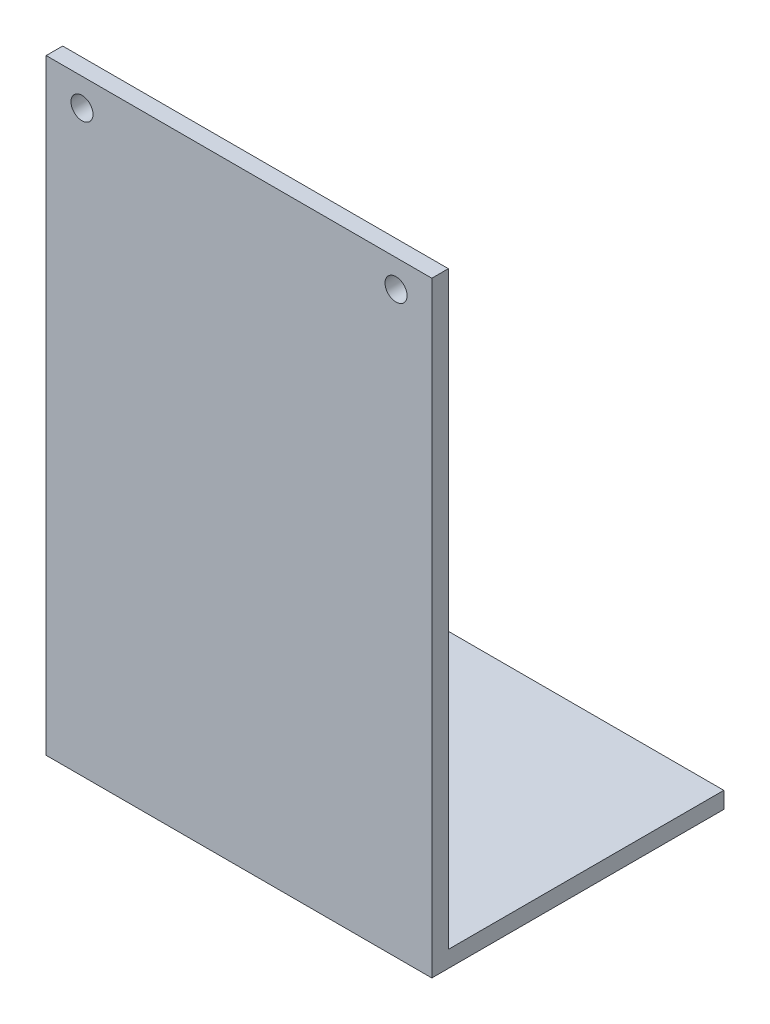
SolidWorks part; units mm, degrees
ref_plane "Front Plane" through (0, 0, 0) normal (0, 0, 1) x (1, 0, 0)
ref_plane "Top Plane" through (0, 0, 0) normal (0, 1, 0) x (1, 0, 0)
ref_plane "Right Plane" through (0, 0, 0) normal (1, 0, 0) x (0, 0, -1)
sketch "Sketch1" plane through (0, 0, 0) normal (0, 0, 1) x (1, 0, 0)
  line L1 (-35, -55) -> (35, -55)
  line L2 (-35, -55) -> (-35, 55)
  line L3 (-35, 55) -> (35, 55)
  line L4 (35, -55) -> (35, 55)
  line L5 (-35, -55) -> (35, 55) construction
  line L6 (-35, 55) -> (35, -55) construction
  point P0 (0, 0)
  dimension "D1" = 70
  dimension "D2" = 110
extrude "Boss-Extrude1" add sketch "Sketch1" along normal blind 3
sketch "Sketch2" plane through (0, 0, 0) normal (0, 0, -1) x (-1, 0, 0)
  line L0 (35, 55) -> (35, -55) construction
  line L1 (-35, -55) -> (35, -55)
  line L2 (-35, -55) -> (-35, -52)
  line L3 (-35, -52) -> (35, -52)
  line L4 (35, -55) -> (35, -52)
  dimension "D1" = 3
extrude "Boss-Extrude2" add sketch "Sketch2" along normal blind 50
sketch "Sketch3" plane through (0, 0, 3) normal (0, 0, 1) x (1, 0, 0)
  line L0 (-35, -55) -> (35, -55) construction
  line L1 (-35, 55) -> (-35, -55) construction
  circle A0 centre (-28.5, 50) radius 2
  circle A1 centre (28.5, 50) radius 2
  dimension "D5" = 4
  dimension "D6" = 4
  dimension "D1" = 105
  dimension "D2" = 105
  dimension "D3" = 57
  dimension "D4" = 6.5
extrude "Cut-Extrude1" cut sketch "Sketch3" against normal up to surface (3 mm away) up to face at (-8.75, 1.5, 0)
